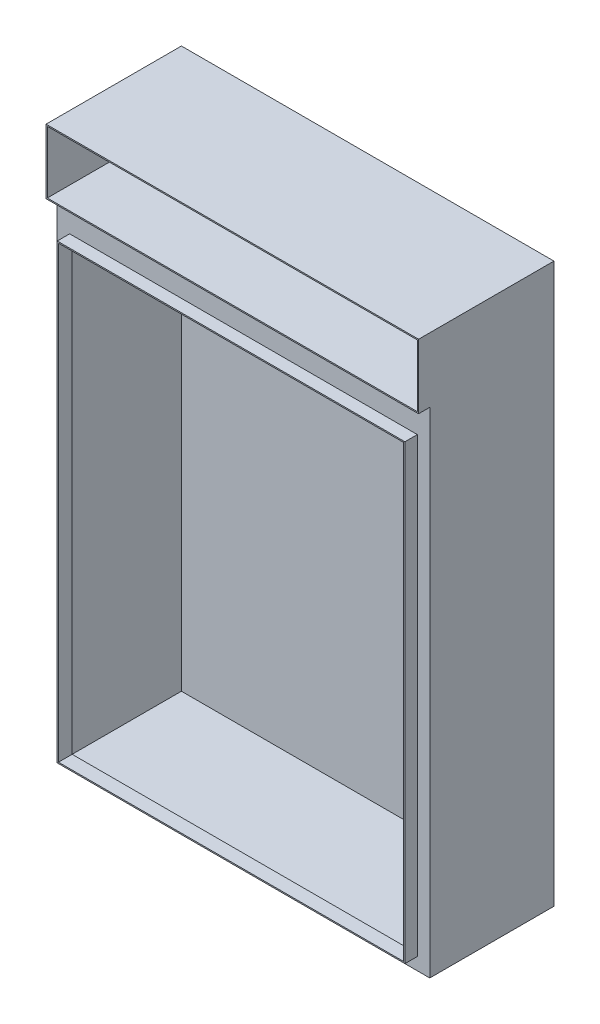
SolidWorks part; units mm, degrees
ref_plane "Front Plane" through (0, 0, 0) normal (0, 0, 1) x (1, 0, 0)
ref_plane "Top Plane" through (0, 0, 0) normal (0, 1, 0) x (1, 0, 0)
ref_plane "Right Plane" through (0, 0, 0) normal (1, 0, 0) x (0, 0, -1)
sketch "Sketch1" plane through (0, 0, 0) normal (0, 0, 1) x (1, 0, 0)
  line L1 (300, -450) -> (-300, -450)
  line L2 (300, -450) -> (300, 450)
  line L3 (300, 450) -> (-300, 450)
  line L4 (-300, -450) -> (-300, 450)
  line L5 (300, -450) -> (-300, 450) construction
  line L6 (300, 450) -> (-300, -450) construction
  point P0 (0, 0)
  dimension "D1" = 600
  dimension "D2" = 900
extrude "Boss-Extrude1" add sketch "Sketch1" along normal blind 200
shell "Shell1" thickness 2
sketch "Sketch2" plane through (0, 0, 2) normal (0, 0, 1) x (1, 0, 0)
  line L0 (0, 0) -> (0, 448) construction
  line L1 (298, 448) -> (-298, 448) construction
  line L2 (-298, 448) -> (-298, -448) construction
  line L3 (298, 346) -> (-298, 346)
  line L4 (298, 346) -> (298, 348)
  line L5 (298, 348) -> (-298, 348)
  line L6 (-298, 346) -> (-298, 348)
  line L7 (298, 346) -> (-298, 348) construction
  line L8 (298, 348) -> (-298, 346) construction
  line L9 (298, 448) -> (-298, 448) construction
  point P5 (0, 347)
  dimension "D1" = 2
  dimension "D2" = 100
extrude "Boss-Extrude2" add sketch "Sketch2" along direction (0, 0, 1) on the side of the normal blind 198
sketch "Sketch3" plane through (0, 0, 200) normal (0, 0, 1) x (1, 0, 0)
  line L1 (-298, 346) -> (298, 346)
  line L2 (-298, 346) -> (-298, -448)
  line L3 (-298, -448) -> (298, -448)
  line L4 (298, 346) -> (298, -448)
  line L5 (-278, 296) -> (278, 296)
  line L6 (-278, 296) -> (-278, -428)
  line L7 (-278, -428) -> (278, -428)
  line L8 (278, 296) -> (278, -428)
  dimension "D1" = 20
  dimension "D2" = 50
  dimension "D3" = 20
  dimension "D4" = 20
extrude "Boss-Extrude3" add sketch "Sketch3" against normal blind 2 contours L2 L1 L4 L3
sketch "Sketch4" plane through (0, 0, 200) normal (0, 0, 1) x (1, 0, 0)
  line L19 (-278, 296) -> (278, 296)
  line L20 (-278, 296) -> (-278, -428)
  line L21 (-278, -428) -> (278, -428)
  line L22 (278, 296) -> (278, -428)
  line L23 (-280, 298) -> (280, 298)
  line L24 (-280, 298) -> (-280, -430)
  line L25 (-280, -430) -> (280, -430)
  line L26 (280, 298) -> (280, -430)
  dimension "D1" = 2
  dimension "D2" = 2
  dimension "D3" = 2
  dimension "D4" = 2
extrude "Boss-Extrude4" add sketch "Sketch4" along normal blind 20
sketch "Sketch5" plane through (0, 0, 200) normal (0, 0, 1) x (1, 0, 0)
  line L0 (300, -450) -> (300, 450) construction
  line L1 (-298, 448) -> (298, 448)
  line L2 (-298, 448) -> (-298, 348)
  line L3 (-298, 348) -> (298, 348)
  line L4 (298, 448) -> (298, 348)
  line L5 (-300, 450) -> (300, 450)
  line L6 (-300, 450) -> (-300, 346)
  line L7 (-300, 346) -> (300, 346)
  line L8 (300, 450) -> (300, 346)
  dimension "D1" = 2
extrude "Boss-Extrude5" add sketch "Sketch5" along normal blind 18
